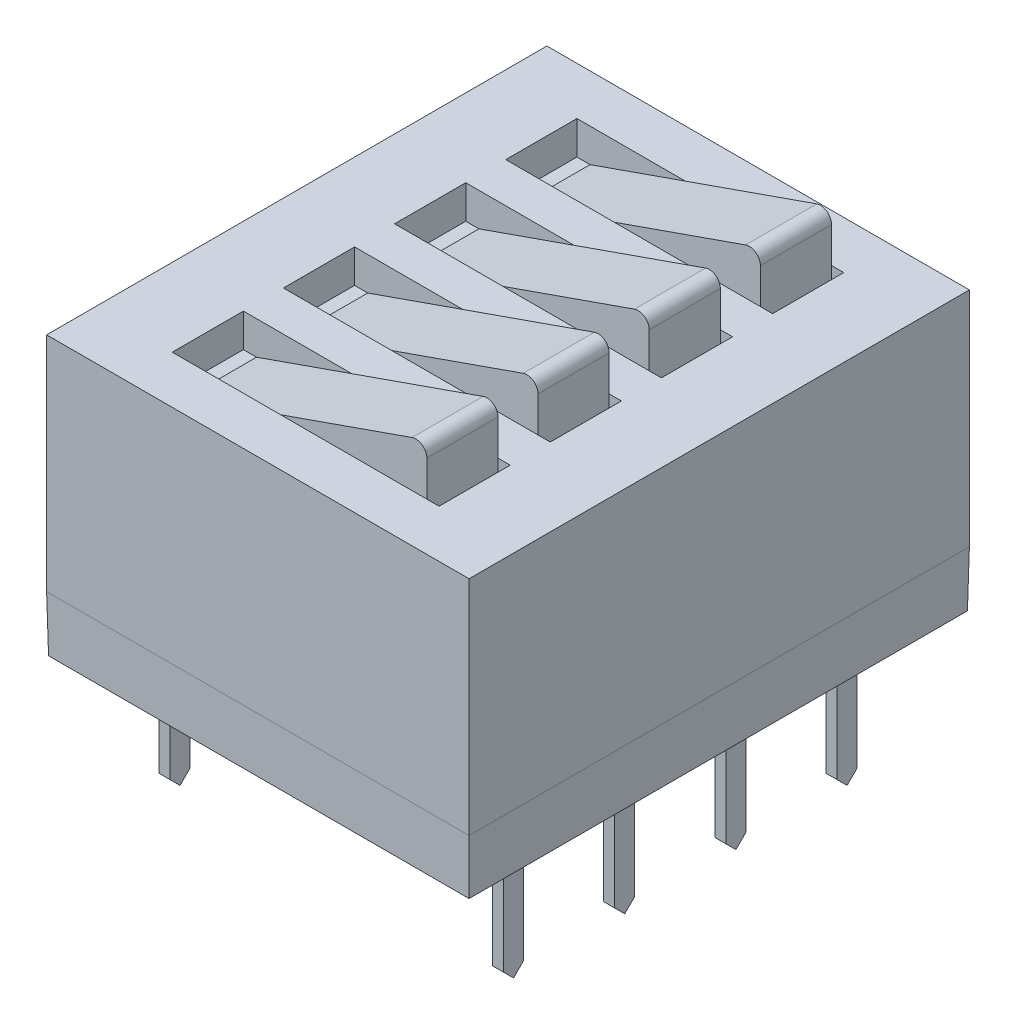
SolidWorks part; units mm, degrees
ref_plane "Front Plane" through (0, 0, 0) normal (0, 0, 1) x (1, 0, 0)
ref_plane "Top Plane" through (0, 0, 0) normal (0, 1, 0) x (1, 0, 0)
ref_plane "Right Plane" through (0, 0, 0) normal (1, 0, 0) x (0, 0, -1)
ref_plane "Plane1" through (0, 0.381, 0) normal (0, 1, 0) x (-1, 0, 0)
sketch "Sketch1" plane through (0, 0.381, 0) normal (0, 1, 0) x (0, 0, -1)
  line L1 (1.905, -8.636) -> (-9.525, -8.636)
  line L2 (1.905, -8.636) -> (1.905, 1.016)
  line L3 (1.905, 1.016) -> (-9.525, 1.016)
  line L4 (-9.525, -8.636) -> (-9.525, 1.016)
  dimension "D1" = 9.525
  dimension "D2" = 1.905
  dimension "D3" = 9.652
  dimension "D4" = 1.016
extrude "Base-Extrude" add sketch "Sketch1" along normal blind 6.35
chamfer "Chamfer1" distance 1.27 angle 1 4 edges at (8.636, 0.381, 3.81) (3.81, 0.381, 9.525) (-1.016, 0.381, 3.81) (3.81, 0.381, -1.905)
ref_plane "Plane2" through (8.636, 0, 0) normal (1, 0, 0) x (0, 0, -1)
ref_plane "Plane3" through (10.541, 0, 0) normal (1, 0, 0) x (0, 0, -1)
sketch "Sketch3" plane through (10.541, 0, 0) normal (0, 0, -1) x (-1, 0, 0)
  line L0 (10.541, 1.4986) -> (10.541, -2.5654)
  line L1 (10.033, 2.0066) -> (9.271, 2.0066)
  arc A0 (10.033, 2.0066) -> (10.541, 1.4986) centre (10.033, 1.4986) cw
  dimension "D2" = 0.762
  dimension "D1" = 0.508
  dimension "D3" = 4.064
  dimension "D4" = 2.5654
extrude "Boss-Extrude-Thin1" add sketch "Sketch3" along normal mid plane 1.27 thin thin type mid plane wall 0.254
sketch "Sketch4" plane through (0.127, 0, 0) normal (1, 0, 0) x (0, 0, -1)
  line L0 (0.635, -2.5654) -> (-0.635, -2.5654) construction
  line L1 (0.635, -2.5654) -> (0.635, 0.381) construction
  line L2 (0.635, -2.5654) -> (0, -2.5654)
  line L3 (0.635, -2.5654) -> (0.635, 0.381)
  line L4 (0.635, 0.381) -> (0.2286, -0.0254)
  line L5 (0.2286, -0.0254) -> (0.2286, -2.3368)
  line L6 (0.2286, -2.3368) -> (0, -2.5654)
  dimension "D1" = 0.4064
  dimension "D2" = 45
extrude "Cut-Extrude1" cut sketch "Sketch4" against normal through all
sketch "Sketch5" plane through (0.127, 0, 0) normal (1, 0, 0) x (0, 0, -1)
  line L0 (-0.635, 0.381) -> (-0.2286, -0.0254)
  line L1 (-9.5028, 0.381) -> (1.8828, 0.381) construction
  line L2 (-0.2286, -0.0254) -> (-0.2286, -2.3368)
  line L3 (-0.2286, -2.3368) -> (0, -2.5654)
  line L4 (0.2286, -2.3368) -> (0, -2.5654) construction
  line L5 (0.635, 0.381) -> (0.2286, -0.0254) construction
  line L6 (-0.635, -2.5654) -> (-0.635, 0.381) construction
  line L7 (0, -2.5654) -> (-0.635, -2.5654) construction
  line L8 (-0.635, -2.5654) -> (-0.635, 0.381)
  line L9 (0, -2.5654) -> (-0.635, -2.5654)
extrude "Cut-Extrude2" cut sketch "Sketch5" against normal through all
pattern_linear "LPattern2" count 4 spacing 2.54 along (0, 0, 1) of "Boss-Extrude-Thin1", "Cut-Extrude2", "Cut-Extrude1"
ref_plane "Plane4" through (3.81, 0, 0) normal (-1, 0, 0) x (0, 0, 1)
mirror "Mirror1" about plane through (3.81, 0, 0) normal (-1, 0, 0) of "LPattern2", "Boss-Extrude-Thin1", "Cut-Extrude1", "Cut-Extrude2"
sketch "Sketch6" plane through (0, 6.731, 0) normal (0, 1, 0) x (-1, 0, 0)
  line L1 (-0.762, 0.8128) -> (-6.858, 0.8128)
  line L2 (-0.762, 0.8128) -> (-0.762, -0.8128)
  line L3 (-0.762, -0.8128) -> (-6.858, -0.8128)
  line L4 (-6.858, 0.8128) -> (-6.858, -0.8128)
  line L5 (-3.81, -1.905) -> (-3.81, 0.8128) construction
  line L6 (-8.636, -1.905) -> (1.016, -1.905) construction
  line L7 (0, 0) -> (-0.762, 0) construction
  dimension "D1" = 6.096
  dimension "D2" = 1.6256
extrude "Cut-Extrude3" cut sketch "Sketch6" against normal blind 0.762
sketch "Sketch7" plane through (0, 0, -0.8128) normal (0, 0, 1) x (1, 0, 0)
  line L0 (1.0626, 5.969) -> (6.2406, 7.7823)
  line L1 (6.5786, 7.5426) -> (6.5786, 5.969)
  line L2 (6.5786, 5.969) -> (1.0626, 5.969)
  line L4 (3.81, 6.9311) -> (3.81, 1.651) construction
  line L5 (-1.016, 1.651) -> (8.636, 1.651) construction
  line L6 (0.762, 5.969) -> (6.858, 5.969) construction
  arc A0 (6.5786, 7.5426) -> (6.2406, 7.7823) centre (6.3246, 7.5426) ccw
  dimension "D1" = 0.254
  dimension "D2" = 5.4864
  dimension "D3" = 19.3
  dimension "D4" = 2.7686
extrude "Boss-Extrude1" add sketch "Sketch7" along normal blind 1.6256
pattern_linear "LPattern3" count 4 spacing 2.54 along (0, 0, 1) of "Cut-Extrude3", "Boss-Extrude1"
sketch "Component_Outline" plane through (0, 0, 0) normal (0, 1, 0) x (1, 0, 0)
  line L1 (-0.9938, -9.5028) -> (8.636, -9.5028)
  line L2 (-0.9938, -9.5028) -> (-0.9938, 1.905)
  line L3 (-0.9938, 1.905) -> (8.636, 1.905)
  line L4 (8.636, -9.5028) -> (8.636, 1.905)
